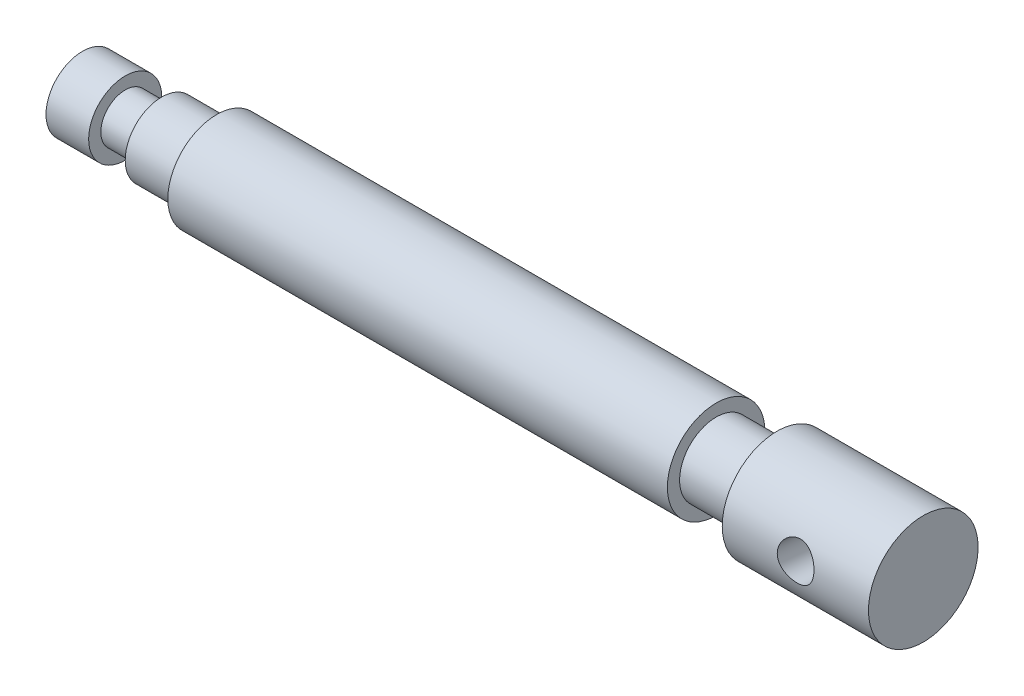
SolidWorks part; units mm, degrees
ref_plane "Front Plane" through (0, 0, 0) normal (0, 0, 1) x (1, 0, 0)
ref_plane "Top Plane" through (0, 0, 0) normal (0, 1, 0) x (1, 0, 0)
ref_plane "Right Plane" through (0, 0, 0) normal (1, 0, 0) x (0, 0, -1)
sketch "Sketch1" plane through (0, 0, 0) normal (0, 0, 1) x (1, 0, 0)
  line L0 (0, 0) -> (0, 6)
  line L1 (0, 6) -> (7, 6)
  line L2 (7, 6) -> (7, 4)
  line L3 (7, 4) -> (13, 4)
  line L4 (13, 4) -> (13, 6)
  line L5 (-8.8837, 0) -> (34.3835, 0) construction
  line L6 (13, 6) -> (22, 6)
  line L7 (22, 6) -> (22, 8)
  line L8 (22, 8) -> (104, 8)
  line L9 (104, 8) -> (104, 6)
  line L10 (104, 6) -> (114, 6)
  line L11 (114, 6) -> (114, 9)
  line L12 (114, 9) -> (138, 9)
  line L13 (138, 9) -> (138, 0)
  line L14 (138, 0) -> (0, 0)
  dimension "D1" = 4
  dimension "D2" = 6
  dimension "D3" = 2
  dimension "D4" = 6
  dimension "D5" = 7
  dimension "D6" = 9
  dimension "D7" = 8
  dimension "D8" = 6
  dimension "D9" = 82
  dimension "D10" = 10
  dimension "D11" = 6
  dimension "D12" = 24
  dimension "D13" = 9
revolve "Revolve1" add sketch "Sketch1" angle 360 about L5
hole_wizard "Ø6.0mm Dowel Hole1" positions "3DSketch1" profile "Sketch3" hole size "Ø6.0" standard "ISO"
sketch3d "3DSketch1"
  point P0 (126, 0.8212, 8.9625)
  dimension "D1" = 12
sketch "Sketch3" plane through (126, 0.8212, 8.9625) normal (1, 0, 0) x (0, -0.9958, 0.0912)
  line L0 (0, 0) -> (0, 77.8026)
  line L1 (0, 77.8026) -> (3, 76)
  line L2 (3, 76) -> (3, 0)
  line L5 (3, 0) -> (0, 0)
  line L10 (0, 77.8026) -> (-3, 76) construction
  line L11 (0, -6.35) -> (0, 107.95) construction
  dimension "Hole Dia." = 6
  dimension "Hole Depth" = 76
  dimension "Drill Angle" = 118
